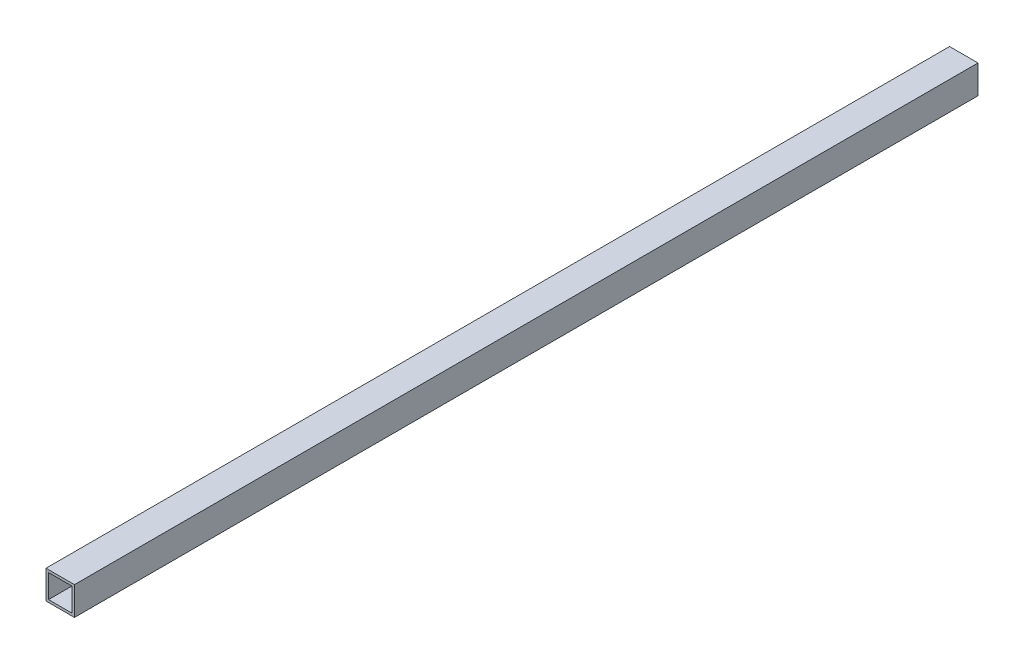
SolidWorks part; units mm, degrees
material "6061 Alloy"
ref_plane "Front Plane" through (0, 0, 0) normal (0, 0, 1) x (1, 0, 0)
ref_plane "Top Plane" through (0, 0, 0) normal (0, 1, 0) x (1, 0, 0)
ref_plane "Right Plane" through (0, 0, 0) normal (1, 0, 0) x (0, 0, -1)
sketch "Sketch1" plane through (0, 0, 0) normal (0, 0, 1) x (1, 0, 0)
  line L1 (-8.5, 8.5) -> (8.5, 8.5)
  line L2 (-8.5, 8.5) -> (-8.5, -8.5)
  line L3 (-8.5, -8.5) -> (8.5, -8.5)
  line L4 (8.5, 8.5) -> (8.5, -8.5)
  line L5 (-8.5, 8.5) -> (8.5, -8.5) construction
  line L6 (-8.5, -8.5) -> (8.5, 8.5) construction
  line L11 (-5.5475, 5.5475) -> (5.5475, -5.5475) construction
  line L12 (-5.5475, -5.5475) -> (5.5475, 5.5475) construction
  line L17 (-7, 7) -> (7, 7)
  line L18 (-7, 7) -> (-7, -7)
  line L19 (-7, -7) -> (7, -7)
  line L20 (7, 7) -> (7, -7)
  line L21 (-7, 7) -> (7, -7) construction
  line L22 (-7, -7) -> (7, 7) construction
  point P0 (0, 0)
  point P6 (0, 0)
  point P11 (0, 0)
  dimension "D1" = 17
  dimension "D2" = 17
  dimension "D3" = 1.5
extrude "Boss-Extrude1" add sketch "Sketch1" along normal blind 540
